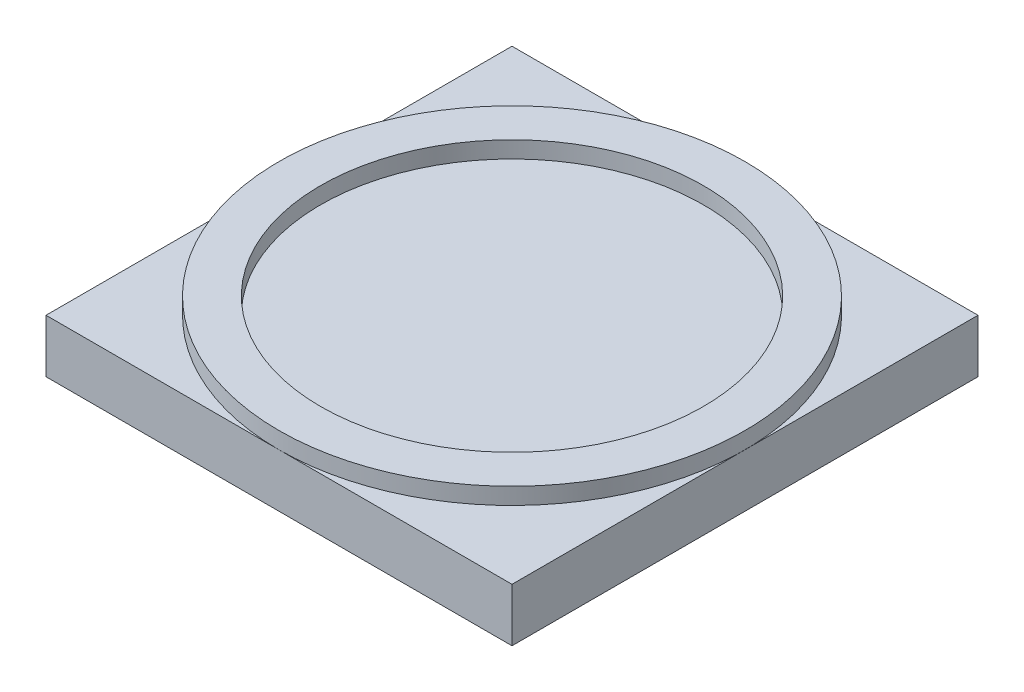
SolidWorks part; units mm, degrees
ref_plane "Front Plane" through (0, 0, 0) normal (0, 0, 1) x (1, 0, 0)
ref_plane "Top Plane" through (0, 0, 0) normal (0, 1, 0) x (1, 0, 0)
ref_plane "Right Plane" through (0, 0, 0) normal (1, 0, 0) x (0, 0, -1)
sketch "Sketch1" plane through (0, 0, 0) normal (0, 1, 0) x (1, 0, 0)
  line L1 (-7, -7) -> (7, -7)
  line L2 (-7, -7) -> (-7, 7)
  line L3 (-7, 7) -> (7, 7)
  line L4 (7, -7) -> (7, 7)
  line L5 (-7, -7) -> (7, 7) construction
  line L6 (-7, 7) -> (7, -7) construction
  point P0 (0, 0)
  dimension "D1" = 14
  dimension "D2" = 14
extrude "Boss-Extrude1" add sketch "Sketch1" along normal blind 1.6
sketch "Sketch2" plane through (0, 1.6, 0) normal (0, 1, 0) x (1, 0, 0)
  circle A0 centre (0, 0) radius 7
  circle A1 centre (0, 0) radius 5.75
  dimension "D1" = 11.5
extrude "Boss-Extrude2" add sketch "Sketch2" along normal blind 0.5 separate body
